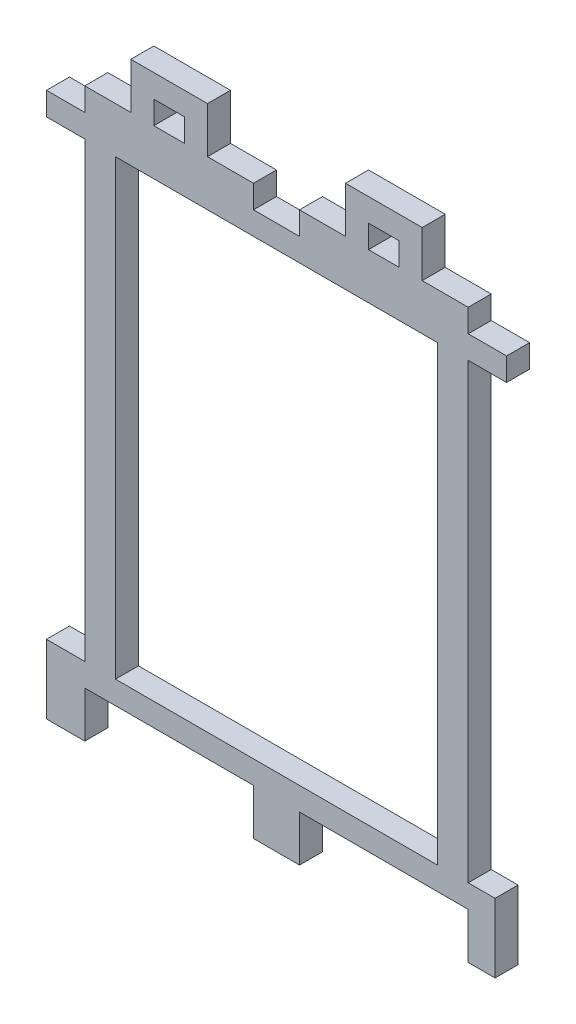
SolidWorks part; units mm, degrees
material "Custom Plastic"
ref_plane "Front Plane" through (0, 0, 0) normal (0, 0, 1) x (1, 0, 0)
ref_plane "Top Plane" through (0, 0, 0) normal (0, 1, 0) x (1, 0, 0)
ref_plane "Right Plane" through (0, 0, 0) normal (1, 0, 0) x (0, 0, -1)
sketch "Sketch1" plane through (0, 0, 0) normal (0, 0, 1) x (1, 0, 0)
  line L46 (0, 0) -> (5, 0)
  line L47 (5, 0) -> (5, 3)
  line L48 (5, 3) -> (27, 3)
  line L49 (27, 3) -> (27, 0)
  line L50 (27, 0) -> (33, 0)
  line L51 (33, 0) -> (33, 3)
  line L52 (33, 3) -> (55, 3)
  line L53 (55, 3) -> (55, 0)
  line L54 (55, 0) -> (60, 0)
  line L55 (60, 0) -> (60, -3)
  line L56 (60, -3) -> (55, -3)
  line L57 (55, -3) -> (55, -62)
  line L58 (55, -62) -> (58.5, -62)
  line L59 (58.5, -62) -> (58.5, -71)
  line L60 (58.5, -71) -> (55, -71)
  line L61 (55, -71) -> (55, -65)
  line L62 (55, -65) -> (33, -65)
  line L63 (33, -65) -> (33, -71)
  line L64 (33, -71) -> (27, -71)
  line L65 (27, -71) -> (27, -65)
  line L66 (27, -65) -> (5, -65)
  line L67 (5, -65) -> (5, -71)
  line L68 (5, -71) -> (0, -71)
  line L69 (0, -71) -> (0, -62)
  line L70 (0, -62) -> (5, -62)
  line L71 (0, 0) -> (0, -3)
  line L72 (0, -3) -> (5, -3)
  line L73 (5, -3) -> (5, -62)
  line L74 (9, -3) -> (9, -62)
  line L75 (9, -62) -> (51, -62)
  line L76 (51, -62) -> (51, -3)
  line L77 (51, -3) -> (9, -3)
  dimension "D10" = 5
  dimension "D11" = 3
  dimension "D12" = 22
  dimension "D13" = 6
  dimension "D14" = 22
  dimension "D15" = 5
  dimension "D16" = 3
  dimension "D17" = 59
  dimension "D18" = 9
  dimension "D19" = 3.5
  dimension "D20" = 3
  dimension "D21" = 22
  dimension "D22" = 6
  dimension "D23" = 4
  dimension "D24" = 4
extrude "Boss-Extrude1" add sketch "Sketch1" along normal blind 3
sketch "Sketch2" plane through (0, 0, 0) normal (0, 0, -1) x (-1, 0, 0)
  line L0 (-55, 3) -> (-33, 3) construction
  line L1 (-49, 3) -> (-39, 3)
  line L2 (-49, 3) -> (-49, 9)
  line L3 (-49, 9) -> (-39, 9)
  line L4 (-39, 3) -> (-39, 9)
  line L5 (-55, 0) -> (-55, 3) construction
  line L6 (-46, 3) -> (-42, 3)
  line L7 (-46, 3) -> (-46, 6)
  line L8 (-46, 6) -> (-42, 6)
  line L9 (-42, 3) -> (-42, 6)
  line L10 (-30, 0) -> (-30, 10.4595) construction
  line L11 (-33, 0) -> (-27, 0) construction
  line L12 (-18, 3) -> (-18, 6)
  line L13 (-14, 6) -> (-18, 6)
  line L14 (-14, 3) -> (-14, 6)
  line L15 (-14, 3) -> (-18, 3)
  line L16 (-21, 3) -> (-21, 9)
  line L17 (-11, 9) -> (-21, 9)
  line L18 (-11, 3) -> (-11, 9)
  line L19 (-11, 3) -> (-21, 3)
  line M13 (-5, 3) -> (-27, 3)
  line M17 (-33, 3) -> (-55, 3)
  dimension "D1" = 6
  dimension "D2" = 3
  dimension "D3" = 3
  dimension "D4" = 3
  dimension "D5" = 10
  dimension "D6" = 6
extrude "Boss-Extrude2" add sketch "Sketch2" against normal blind 3 contours L9 L4 L3 L2 L7 L8 M17 | L18 L17 L16 L12 L13 L14 M13
